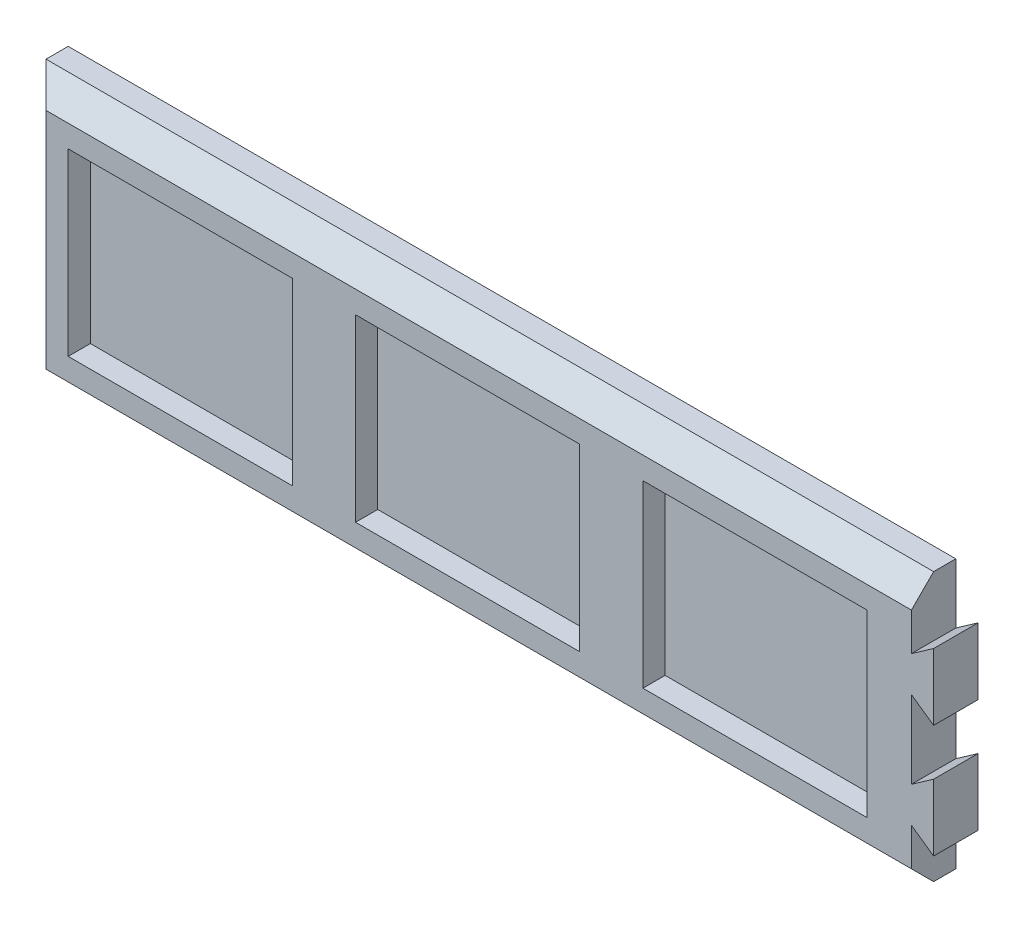
SolidWorks part; units mm, degrees
ref_plane "Ebene vorne" through (0, 0, 0) normal (0, 0, 1) x (1, 0, 0)
ref_plane "Ebene oben" through (0, 0, 0) normal (0, 1, 0) x (1, 0, 0)
ref_plane "Ebene rechts" through (0, 0, 0) normal (1, 0, 0) x (0, 0, -1)
sketch "Skizze1" plane through (0, 0, 0) normal (0, 0, 1) x (1, 0, 0)
  line L0 (-69.3021, 0) -> (239.636, 0) construction
  line L1 (0, 30.25) -> (200, 30.25)
  line L2 (0, 30.25) -> (0, -30.25)
  line L3 (0, -30.25) -> (200, -30.25)
  line L4 (200, 30.25) -> (200, -30.25)
  dimension "D1" = 60.5
  dimension "D2" = 200
extrude "Aufsatz-Linear austragen1" add sketch "Skizze1" along normal blind 10
sketch "Skizze2" plane through (0, 0, 10) normal (0, 0, 1) x (1, 0, 0)
  line L0 (-60.4178, 0) -> (224.8404, 0) construction
  line L1 (10, 20.25) -> (60.5, 20.25)
  line L2 (10, 20.25) -> (10, -20.25)
  line L3 (10, -20.25) -> (60.5, -20.25)
  line L4 (60.5, 20.25) -> (60.5, -20.25)
  line L5 (0, 30.25) -> (0, -30.25) construction
  line L6 (74.75, 20.25) -> (74.75, -20.25)
  line L7 (74.75, 20.25) -> (125.25, 20.25)
  line L8 (125.25, 20.25) -> (125.25, -20.25)
  line L9 (74.75, -20.25) -> (125.25, -20.25)
  line L10 (139.5, 20.25) -> (139.5, -20.25)
  line L11 (139.5, 20.25) -> (190, 20.25)
  line L12 (190, 20.25) -> (190, -20.25)
  line L13 (139.5, -20.25) -> (190, -20.25)
  line L14 (200, -30.25) -> (200, 30.25) construction
  dimension "D1" = 40.5
  dimension "D2" = 50.5
  dimension "D3" = 10
  dimension "D5" = 40.5
  dimension "D6" = 10
  dimension "D4" = 3
extrude "Schnitt-Linear austragen1" cut sketch "Skizze2" against normal blind 5
chamfer "Fase1" distance 5 angle 45 3 edges at (100, -30.25, 10) (0, 0, 10) (100, 30.25, 10)
sketch "Skizze3" plane through (0, 0, 10) normal (0, 0, 1) x (1, 0, 0)
  line L0 (200, 16.75) -> (205, 20.25)
  line L1 (200, -25.25) -> (200, 25.25) construction
  line L2 (205, 20.25) -> (205, 5.25)
  line L3 (205, 5.25) -> (200, 8.75)
  line L4 (214.4969, 12.75) -> (194.4563, 12.75) construction
  line L5 (200, -8.75) -> (205, -5.25)
  line L6 (205, -20.25) -> (200, -16.75)
  line L7 (205, -5.25) -> (205, -20.25)
  line L8 (200, 16.75) -> (200, 8.75)
  line L9 (200, -8.75) -> (200, -16.75)
  dimension "D1" = 5
  dimension "D2" = 15
  dimension "D3" = 8
  dimension "D4" = 10
  dimension "D6" = 10
  dimension "D5" = 2
extrude "Aufsatz-Linear austragen2" add sketch "Skizze3" against normal blind 10
